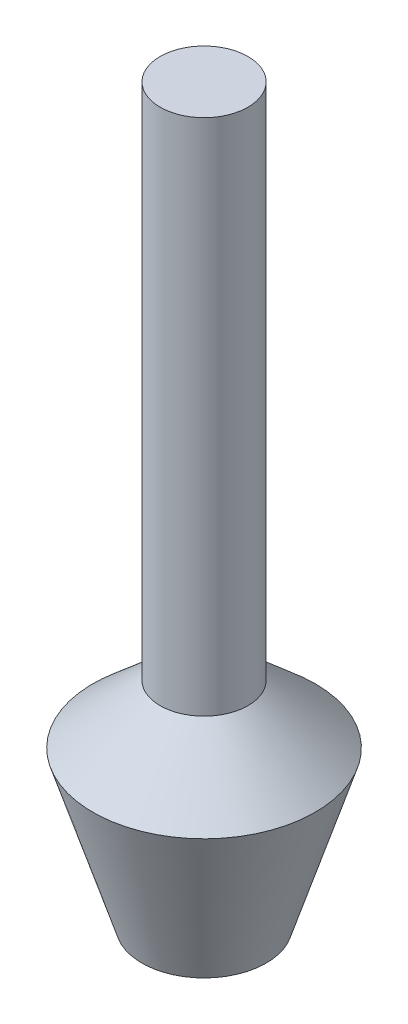
SolidWorks part; units mm, degrees
material "Plain Carbon Steel"
ref_plane "Plane1" through (0, 0, 0) normal (0, 0, 1) x (1, 0, 0)
ref_plane "Plane2" through (0, 0, 0) normal (0, 1, 0) x (-1, 0, 0)
ref_plane "Plane3" through (0, 0, 0) normal (1, 0, 0) x (0, 0, -1)
sketch "Sketch1" plane through (0, 0, 0) normal (0, 0, 1) x (1, 0, 0)
  line L0 (0, 0) -> (0, 91.3243) construction
  line L1 (3.81, 63.5) -> (3.81, 18.542)
  line L2 (0, 63.5) -> (3.81, 63.5)
  line L3 (0, 0) -> (5.3975, 0)
  line L4 (9.652, 13.462) -> (5.3975, 0)
  line L5 (9.652, 13.462) -> (3.81, 18.542)
  line L6 (0, 63.5) -> (0, 0)
  dimension "D1" = 18.542
  dimension "D2" = 10.795
  dimension "D3" = 19.304
  dimension "D4" = 7.62
  dimension "D5" = 13.462
  dimension "D6" = 63.5
revolve "Base-Revolve" add sketch "Sketch1" angle 360 about L0
